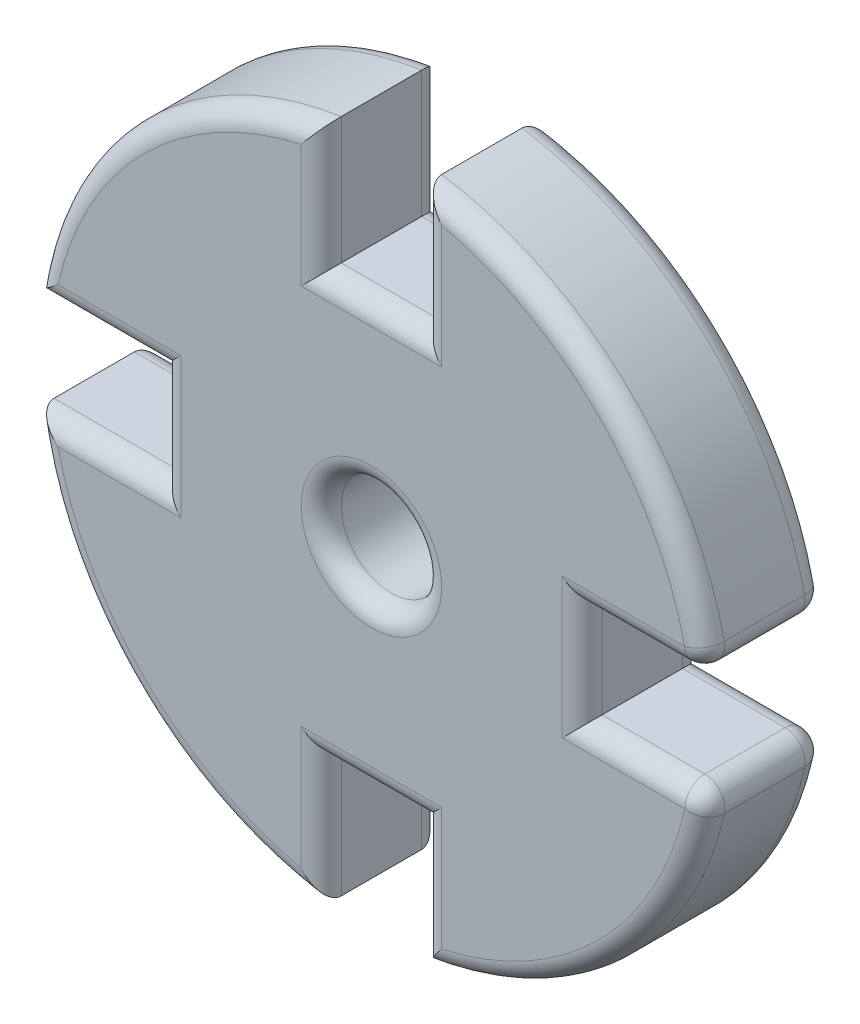
SolidWorks part; units mm, degrees
ref_plane "Front Plane" through (0, 0, 0) normal (0, 0, 1) x (1, 0, 0)
ref_plane "Top Plane" through (0, 0, 0) normal (0, 1, 0) x (1, 0, 0)
ref_plane "Right Plane" through (0, 0, 0) normal (1, 0, 0) x (0, 0, -1)
sketch "Sketch1" plane through (0, 0, 0) normal (0, 0, 1) x (1, 0, 0)
  line L0 (0, 0) -> (-29.2239, 0) construction
  line L1 (0, 0) -> (0, 50000) construction
  line L2 (0, 0) -> (50000, 0) construction
  line L3 (2.5, 10.5) -> (2.5, 16.8152)
  line L4 (-10.5, -2.5) -> (-16.8152, -2.5)
  line L5 (-10.5, -2.5) -> (-10.5, 2.5)
  line L6 (-10.5, 2.5) -> (-16.8152, 2.5)
  line L7 (-2.5, 10.5) -> (2.5, 10.5)
  line L8 (-10.5, -2.5) -> (-17, 0) construction
  line L9 (-10.5, 2.5) -> (-17, 0) construction
  line L10 (-2.5, 10.5) -> (-2.5, 16.8152)
  line L11 (10.5, -2.5) -> (16.8152, -2.5)
  line L12 (10.5, 2.5) -> (10.5, -2.5)
  line L13 (10.5, 2.5) -> (16.8152, 2.5)
  line L14 (-2.5, -10.5) -> (-2.5, -16.8152)
  line L15 (2.5, -10.5) -> (-2.5, -10.5)
  line L16 (2.5, -10.5) -> (2.5, -16.8152)
  circle A0 centre (0, 0) radius 17
  circle A1 centre (0, 0) radius 2.5
  point P3 (-17, 0)
  dimension "D1" = 34
  dimension "D3" = 5
  dimension "D2" = 5
extrude "Extrude1" add sketch "Sketch1" along normal blind 6 contours L13 A0 L3 L7 L10 L6 L5 L4 L14 L15 L16 L11 L12 A1
fillet "Fillet1" radius 1 36 edges at (10.5, 0, 6) (13.6576, -2.5, 6) (12.0208, -12.0208, 6) (2.5, -13.6576, 6) (0, -10.5, 6) (-2.5, -13.6576, 6) (-12.0208, -12.0208, 6) (-13.6576, -2.5, 6) (-10.5, 0, 6) (-13.6576, 2.5, 6) (-12.0208, 12.0208, 6) (-2.5, 13.6576, 6) (0, 10.5, 6) (2.5, 13.6576, 6) (12.0208, 12.0208, 6) (13.6576, 2.5, 6) (2.5, 0, 6) (12.0208, 12.0208, 0) (2.5, 13.6576, 0) (0, 10.5, 0) (-2.5, 13.6576, 0) (-12.0208, 12.0208, 0) (-13.6576, 2.5, 0) (-10.5, 0, 0) (-13.6576, -2.5, 0) (-12.0208, -12.0208, 0) (-2.5, -13.6576, 0) (0, -10.5, 0) (2.5, -13.6576, 0) (12.0208, -12.0208, 0) (13.6576, -2.5, 0) (10.5, 0, 0) (13.6576, 2.5, 0) (2.5, 0, 0) (16.8152, -2.5, 3) (16.8152, 2.5, 3)
